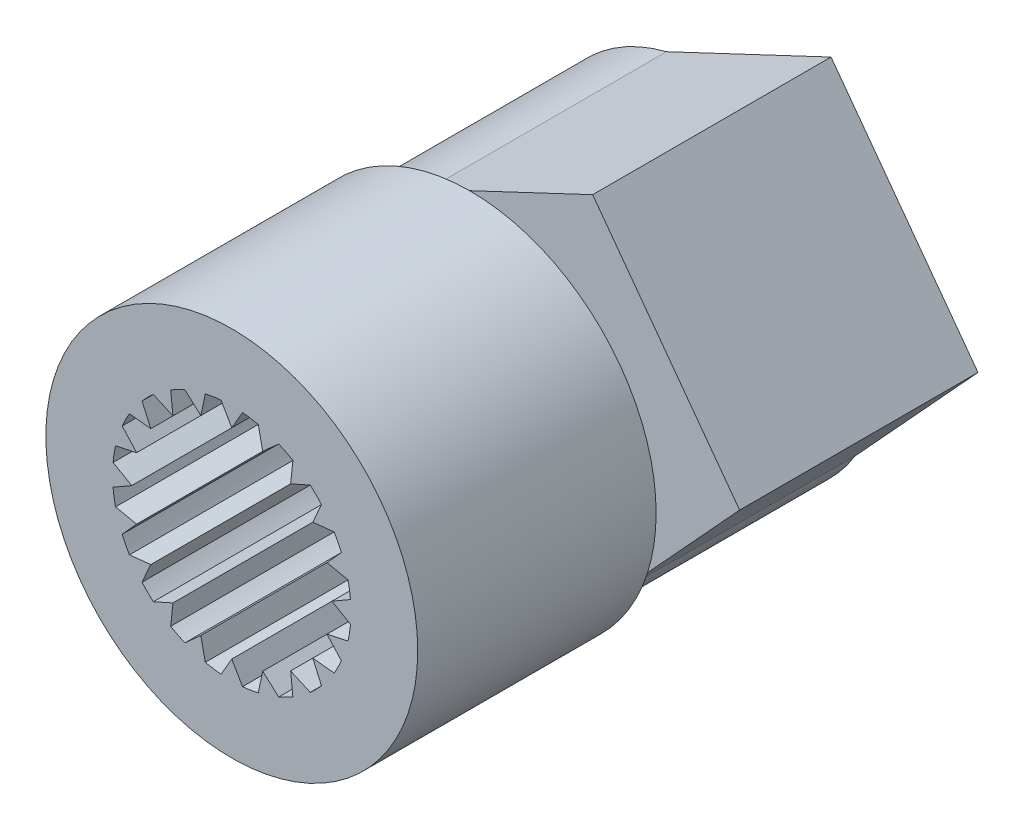
SolidWorks part; units mm, degrees
ref_plane "Front Plane" through (0, 0, 0) normal (0, 0, 1) x (1, 0, 0)
ref_plane "Top Plane" through (0, 0, 0) normal (0, 1, 0) x (1, 0, 0)
ref_plane "Right Plane" through (0, 0, 0) normal (1, 0, 0) x (0, 0, -1)
ref_plane "Plane1" through (12.4375, -0.5553, -0.5) normal (0, 0, -1) x (-1, 0, 0)
sketch "Sketch3" plane through (0, 0, 0) normal (0, 0, 1) x (1, 0, 0)
  line L0 (10, 2.1) -> (9.7749, 2.4898)
  line L1 (9.4447, 2.4375) -> (9.3511, 1.9972)
  line L2 (9.3511, 1.9972) -> (9.0165, 2.2984)
  line L3 (8.118, 1.6456) -> (8.3011, 1.2343)
  line L4 (8.3011, 1.2343) -> (7.8534, 1.2814)
  line L5 (7.7016, 0.9835) -> (8.0028, 0.6489)
  line L6 (8.0028, 0.6489) -> (7.5625, 0.5553)
  line L7 (7.5102, 0.2251) -> (7.9, 0)
  line L8 (7.9, 0) -> (7.5102, -0.2251)
  line L9 (7.5625, -0.5553) -> (8.0028, -0.6489)
  line L10 (8.0028, -0.6489) -> (7.7016, -0.9835)
  line L11 (7.8534, -1.2814) -> (8.3011, -1.2343)
  line L12 (8.3011, -1.2343) -> (8.118, -1.6456)
  line L13 (8.3544, -1.882) -> (8.7657, -1.6989)
  line L14 (8.7657, -1.6989) -> (8.7186, -2.1466)
  line L15 (9.0165, -2.2984) -> (9.3511, -1.9972)
  line L16 (9.3511, -1.9972) -> (9.4447, -2.4375)
  line L17 (9.7749, -2.4898) -> (10, -2.1)
  line L18 (10, -2.1) -> (10.2251, -2.4898)
  line L19 (10.5553, -2.4375) -> (10.6489, -1.9972)
  line L20 (10.6489, -1.9972) -> (10.9835, -2.2984)
  line L21 (11.2814, -2.1466) -> (11.2343, -1.6989)
  line L22 (10, 2.1) -> (10.2251, 2.4898)
  line L23 (10.5553, 2.4375) -> (10.6489, 1.9972)
  line L24 (10.6489, 1.9972) -> (10.9835, 2.2984)
  line L25 (11.2814, 2.1466) -> (11.2343, 1.6989)
  line L26 (11.2343, 1.6989) -> (11.6456, 1.882)
  line L27 (11.882, 1.6456) -> (11.6989, 1.2343)
  line L28 (11.6989, 1.2343) -> (12.1466, 1.2814)
  line L29 (12.2984, 0.9835) -> (11.9972, 0.6489)
  line L30 (11.9972, 0.6489) -> (12.4375, 0.5553)
  line L31 (12.4898, 0.2251) -> (12.1, 0)
  line L32 (12.1, 0) -> (12.4898, -0.2251)
  line L33 (12.4375, -0.5553) -> (11.9972, -0.6489)
  line L34 (11.9972, -0.6489) -> (12.2984, -0.9835)
  line L35 (12.1466, -1.2814) -> (11.6989, -1.2343)
  line L36 (11.6989, -1.2343) -> (11.882, -1.6456)
  line L37 (11.6456, -1.882) -> (11.2343, -1.6989)
  line L38 (8.7186, 2.1466) -> (8.7657, 1.6989)
  line L39 (8.7657, 1.6989) -> (8.3544, 1.882)
  arc A0 (9.0165, 2.2984) -> (8.7186, 2.1466) centre (10, 0) ccw
  arc A1 (8.3544, 1.882) -> (8.118, 1.6456) centre (10, 0) ccw
  arc A2 (7.8534, 1.2814) -> (7.7016, 0.9835) centre (10, 0) ccw
  arc A3 (7.5625, 0.5553) -> (7.5102, 0.2251) centre (10, 0) ccw
  arc A4 (7.5102, -0.2251) -> (7.5625, -0.5553) centre (10, 0) ccw
  arc A5 (7.7016, -0.9835) -> (7.8534, -1.2814) centre (10, 0) ccw
  arc A6 (8.118, -1.6456) -> (8.3544, -1.882) centre (10, 0) ccw
  arc A7 (8.7186, -2.1466) -> (9.0165, -2.2984) centre (10, 0) ccw
  arc A8 (9.4447, -2.4375) -> (9.7749, -2.4898) centre (10, 0) ccw
  arc A9 (10.2251, -2.4898) -> (10.5553, -2.4375) centre (10, 0) ccw
  arc A10 (10.9835, -2.2984) -> (11.2814, -2.1466) centre (10, 0) ccw
  arc A11 (11.6456, -1.882) -> (11.882, -1.6456) centre (10, 0) ccw
  arc A12 (12.1466, -1.2814) -> (12.2984, -0.9835) centre (10, 0) ccw
  arc A13 (12.4375, -0.5553) -> (12.4898, -0.2251) centre (10, 0) ccw
  arc A14 (12.4898, 0.2251) -> (12.4375, 0.5553) centre (10, 0) ccw
  arc A15 (11.882, 1.6456) -> (11.6456, 1.882) centre (10, 0) ccw
  arc A16 (11.2814, 2.1466) -> (10.9835, 2.2984) centre (10, 0) ccw
  arc A17 (10.5553, 2.4375) -> (10.2251, 2.4898) centre (10, 0) ccw
  arc A18 (9.7749, 2.4898) -> (9.4447, 2.4375) centre (10, 0) ccw
  arc A20 (12.2984, 0.9835) -> (12.1466, 1.2814) centre (10, 0) ccw
  circle A21 centre (10, 0) radius 3.9
  dimension "D1" = 7.8
extrude "Boss-Extrude1" add sketch "Sketch3" against normal blind 5
sketch "Sketch5" plane through (0, 0, -5) normal (0, 0, -1) x (-1, 0, 0)
  circle A0 centre (-10, 0) radius 3.6
  circle A1 centre (-10, 0) radius 3.9 construction
  dimension "D1" = 7.2
extrude "Boss-Extrude2" add sketch "Sketch5" along normal blind 5
sketch "Sketch6" plane through (0, 0, -10) normal (0, 0, -1) x (-1, 0, 0)
  line L3 (-9.1185, 3.4904) -> (-12.5691, 5.1186)
  line L4 (-12.5691, 5.1186) -> (-15.6511, 0.9303)
  line L5 (-15.6511, 0.9303) -> (-13.0703, -1.8798)
  line L6 (-13.0703, -1.8798) -> (-15.6511, 0.9303)
  arc A0 (-9.1185, 3.4904) -> (-13.0703, -1.8798) centre (-10, 0) ccw
  circle A1 centre (-10, 0) radius 3.6 construction
  circle M4 centre (-10, 0) radius 3.6
  dimension "D1" = 0.8815
  dimension "D2" = 2.5691
  dimension "D3" = 3.0703
  dimension "D4" = 5.6511
  dimension "D5" = 0.9303
extrude "Boss-Extrude3" add sketch "Sketch6" against normal blind 5 contours L4 L5 L3 M4
sketch "Sketch7" plane through (0, 0, -10) normal (0, 0, -1) x (-1, 0, 0)
  circle A0 centre (-10, 0) radius 1.25
  arc A1 (-13.0703, -1.8798) -> (-9.1185, 3.4904) centre (-10, 0) ccw construction
  dimension "D1" = 2.5
extrude "Cut-Extrude1" cut sketch "Sketch7" against normal through all
